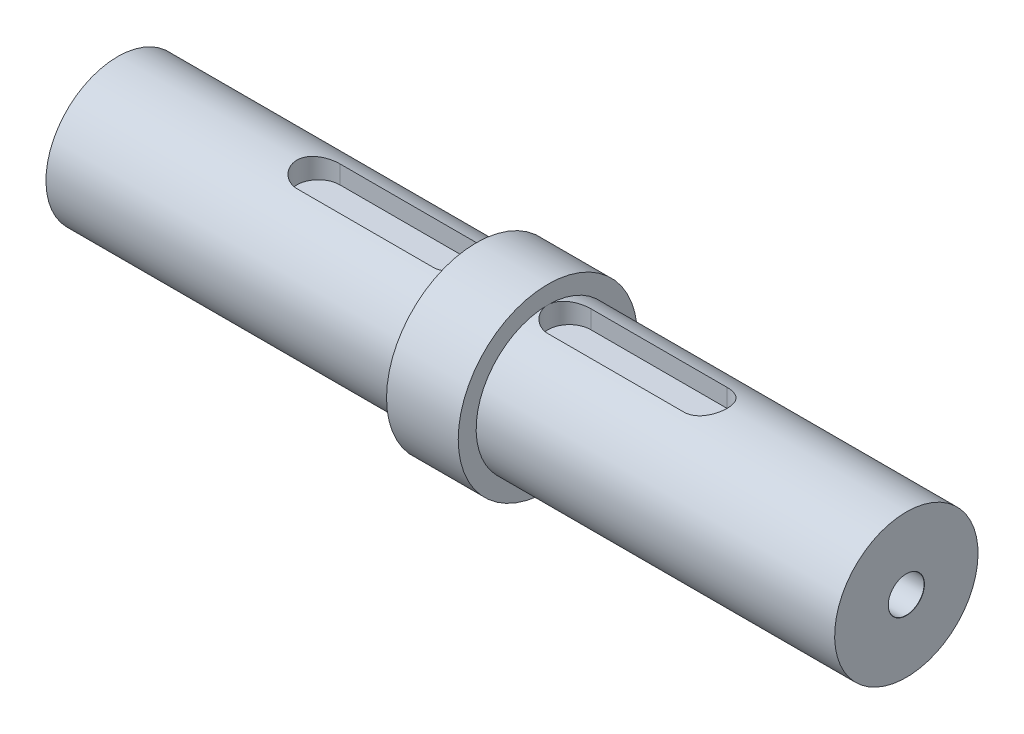
SolidWorks part; units mm, degrees
ref_plane "Front Plane" through (0, 0, 0) normal (0, 0, 1) x (1, 0, 0)
ref_plane "Top Plane" through (0, 0, 0) normal (0, 1, 0) x (1, 0, 0)
ref_plane "Right Plane" through (0, 0, 0) normal (1, 0, 0) x (0, 0, -1)
sketch "Sketch1" plane through (0, 0, 0) normal (0, 0, 1) x (1, 0, 0)
  line L0 (0, 0) -> (0, 10)
  line L1 (0, 10) -> (50, 10)
  line L2 (50, 10) -> (50, 12.5)
  line L3 (50, 12.5) -> (60, 12.5)
  line L4 (60, 12.5) -> (60, 10)
  line L5 (60, 10) -> (110, 10)
  line L6 (110, 10) -> (110, 0)
  line L7 (110, 0) -> (0, 0)
  dimension "D1" = 10
  dimension "D2" = 10
  dimension "D3" = 50
  dimension "D4" = 50
  dimension "D5" = 12.5
  dimension "D6" = 10
revolve "Revolve1" add sketch "Sketch1" angle 360 about L7
ref_plane "Plane1" through (0, 10, 0) normal (0, 1, 0) x (1, 0, 0)
sketch "Sketch2" plane through (0, 10, 0) normal (0, 1, 0) x (1, 0, 0)
  line L0 (47, 0) -> (28, 0) construction
  line L1 (47, -3) -> (28, -3)
  line L2 (47, 3) -> (28, 3)
  line L3 (63, 0) -> (82, 0) construction
  line L4 (63, 3) -> (82, 3)
  line L5 (63, -3) -> (82, -3)
  line L6 (50, 10) -> (50, -10) construction
  line L7 (60, -10) -> (60, 10) construction
  line L8 (50, 12.5) -> (50, -12.5) construction
  arc A0 (47, -3) -> (47, 3) centre (47, 0) ccw
  arc A1 (28, 3) -> (28, -3) centre (28, 0) ccw
  arc A2 (63, 3) -> (63, -3) centre (63, 0) ccw
  arc A3 (82, -3) -> (82, 3) centre (82, 0) ccw
  point P3 (37.5, 0)
  point P8 (72.5, 0)
  point P19 (25, 0)
  dimension "D1" = 6
  dimension "D2" = 6
  dimension "D3" = 25
extrude "Cut-Extrude1" cut sketch "Sketch2" against normal blind 3
hole_wizard "Ø5.0mm Dowel Hole1" positions "3DSketch1" profile "Sketch3" hole size "Ø5.0" standard "ISO"
sketch3d "3DSketch1"
  point P0 (0, 0, 0)
  point P3 (0, 0, 0)
  point P5 (110, 0, 0)
  dimension "D1" = 0
  dimension "D2" = 0
  dimension "D3" = 0
  dimension "D4" = 0
sketch "Sketch3" plane through (110, 0, 0) normal (0, 1, 0) x (0, 0, -1)
  line L0 (0, 0) -> (0, 11.5022)
  line L1 (0, 11.5022) -> (2.5, 10)
  line L2 (2.5, 10) -> (2.5, 0.025)
  line L3 (2.5, 0.025) -> (2.525, 0)
  line L5 (2.525, 0) -> (0, 0)
  line L6 (-2.5, 0.025) -> (-2.525, 0) construction
  line L10 (0, 11.5022) -> (-2.5, 10) construction
  line L11 (0, -6.35) -> (0, 107.95) construction
  dimension "Hole Dia." = 5
  dimension "Hole Depth" = 10
  dimension "Near C'Sink Dia." = 5.05
  dimension "Near C'Sink Angle" = 90
  dimension "Drill Angle" = 118
